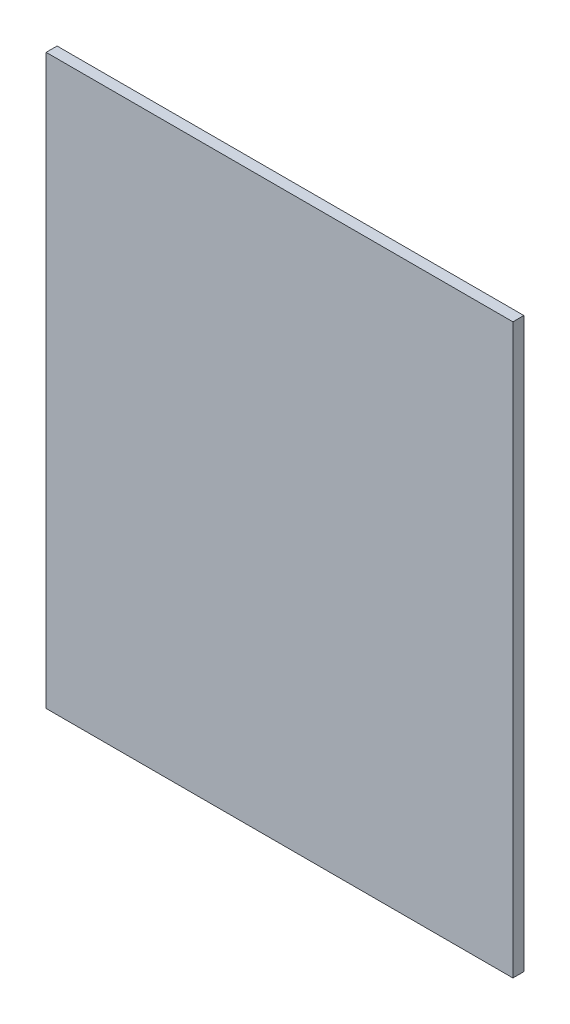
SolidWorks part; units mm, degrees
ref_plane "Front Plane" through (0, 0, 0) normal (0, 0, 1) x (1, 0, 0)
ref_plane "Top Plane" through (0, 0, 0) normal (0, 1, 0) x (1, 0, 0)
ref_plane "Right Plane" through (0, 0, 0) normal (1, 0, 0) x (0, 0, -1)
sketch "Sketch2" plane through (0, 0, 0) normal (0, 0, 1) x (1, 0, 0)
  line L0 (151.8841, -292.9262) -> (36.8841, -292.9262)
  line L1 (151.8841, -292.9262) -> (151.8841, -432.9262)
  line L2 (36.8841, -292.9262) -> (36.8841, -432.9262)
  line L3 (151.8841, -432.9262) -> (36.8841, -432.9262)
  dimension "D1" = 115
  dimension "D2" = 140
extrude "Boss-Extrude1" add sketch "Sketch2" along normal blind 2.7
